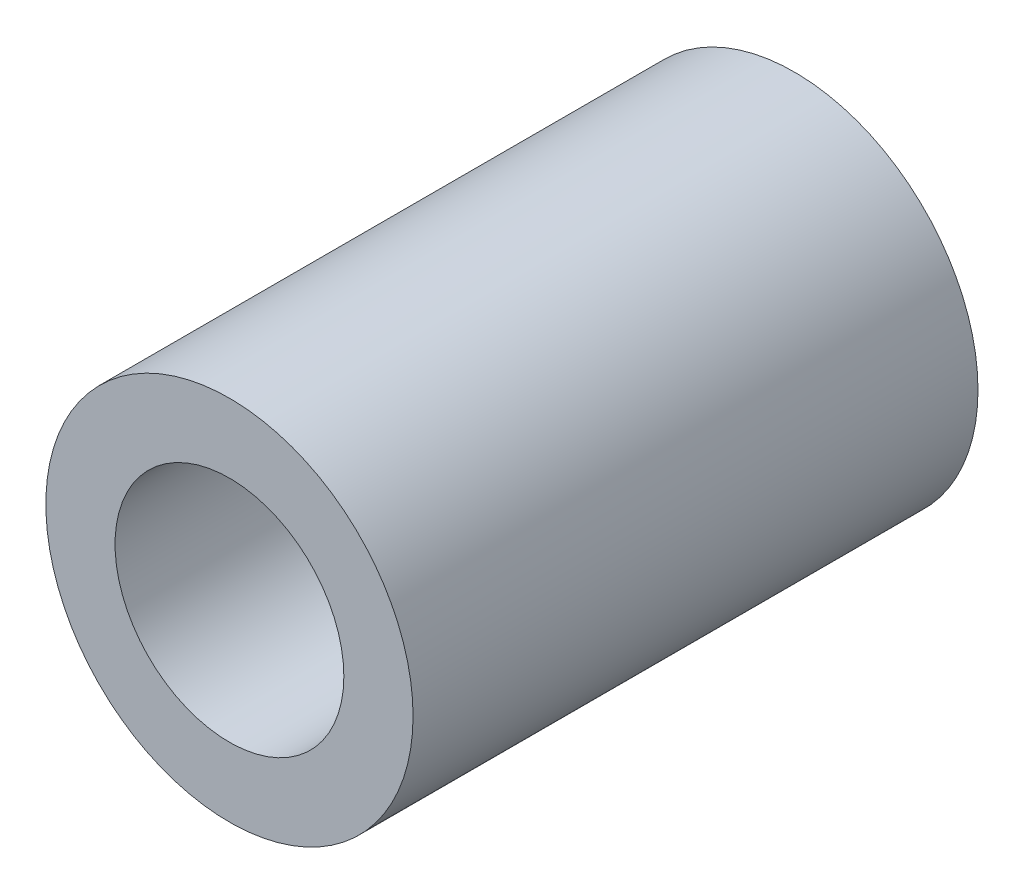
SolidWorks part; units mm, degrees
ref_plane "Alzado" through (0, 0, 0) normal (0, 0, 1) x (1, 0, 0)
ref_plane "Planta" through (0, 0, 0) normal (0, 1, 0) x (1, 0, 0)
ref_plane "Vista lateral" through (0, 0, 0) normal (1, 0, 0) x (0, 0, -1)
sketch "Croquis1" plane through (0, 0, 0) normal (0, 0, 1) x (1, 0, 0)
  circle A0 centre (0, 0) radius 6.5
  circle A1 centre (0, 0) radius 4.05
  dimension "D1" = 13
  dimension "D2" = 8.1
extrude "Saliente-Extruir1" add sketch "Croquis1" along normal blind 20
